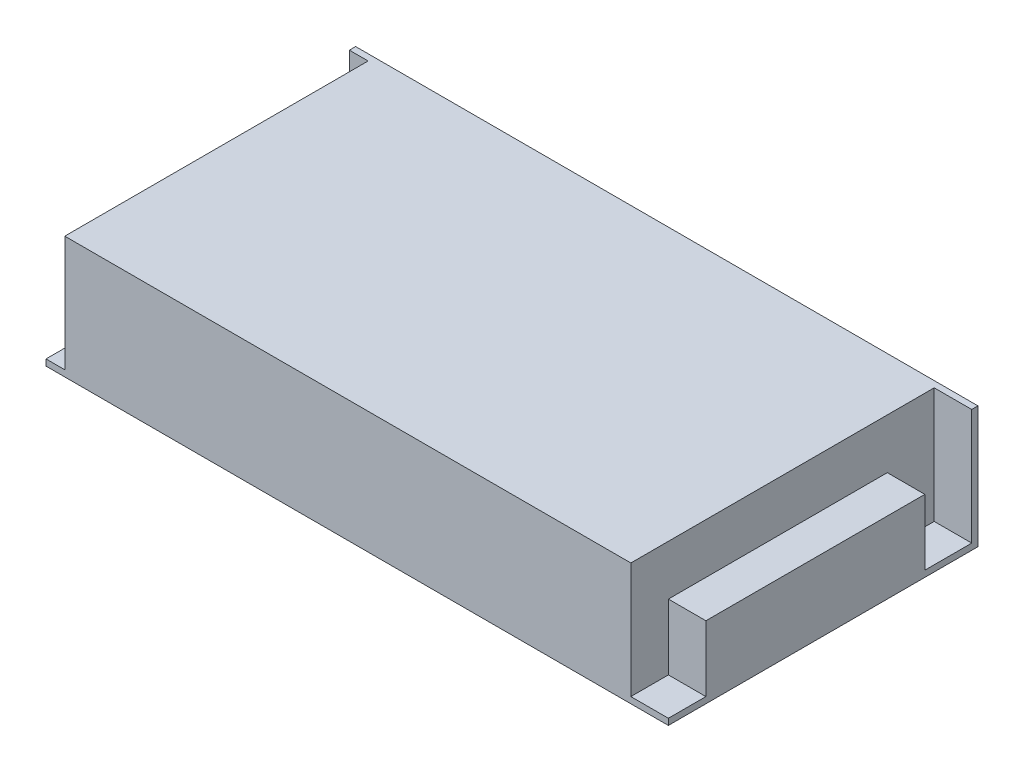
SolidWorks part; units mm, degrees
ref_plane "Спереди" through (0, 0, 0) normal (0, 0, 1) x (1, 0, 0)
ref_plane "Сверху" through (0, 0, 0) normal (0, 1, 0) x (1, 0, 0)
ref_plane "Справа" through (0, 0, 0) normal (1, 0, 0) x (0, 0, -1)
sketch "Эскиз1" plane through (0, 0, 0) normal (0, 1, 0) x (1, 0, 0)
  line L1 (0, 0) -> (199, 0)
  line L2 (0, 0) -> (0, 99)
  line L3 (0, 99) -> (199, 99)
  line L4 (199, 0) -> (199, 99)
  dimension "D1" = 199
  dimension "D2" = 99
extrude "Бобышка-Вытянуть1" add sketch "Эскиз1" along normal blind 39
sketch "Эскиз2" plane through (0, 39, 0) normal (0, 1, 0) x (1, 0, 0)
  line L0 (0, 99) -> (0, 0) construction
  line L1 (0, 97) -> (6, 97)
  line L2 (0, 97) -> (0, 0)
  line L3 (0, 0) -> (6, 0)
  line L4 (6, 97) -> (6, 0)
  line L5 (0, 0) -> (199, 0) construction
  line L6 (199, 99) -> (0, 99) construction
  line L8 (199, 0) -> (187, 0)
  line L9 (199, 0) -> (199, 97)
  line L10 (199, 97) -> (187, 97)
  line L11 (187, 0) -> (187, 97)
  dimension "D1" = 6
  dimension "D2" = 2
  dimension "D3" = 12
extrude "Вырез-Вытянуть1" cut sketch "Эскиз2" against normal offset from surface (37 mm away) 2 up to face at (99.5, 0, -49.5)
sketch "Эскиз3" plane through (187, 0, 0) normal (1, 0, 0) x (0, 0, -1)
  line L0 (0, 0) -> (99, 0) construction
  line L1 (0, 2) -> (0, 39) construction
  line L2 (12, 0) -> (82, 0)
  line L3 (12, 0) -> (12, 23)
  line L4 (12, 23) -> (82, 23)
  line L5 (82, 0) -> (82, 23)
  dimension "D1" = 70
  dimension "D2" = 23
  dimension "D3" = 12
extrude "Бобышка-Вытянуть2" add sketch "Эскиз3" along normal up to surface (12 mm away) up to face at (199, 13.6667, -65.3333)
